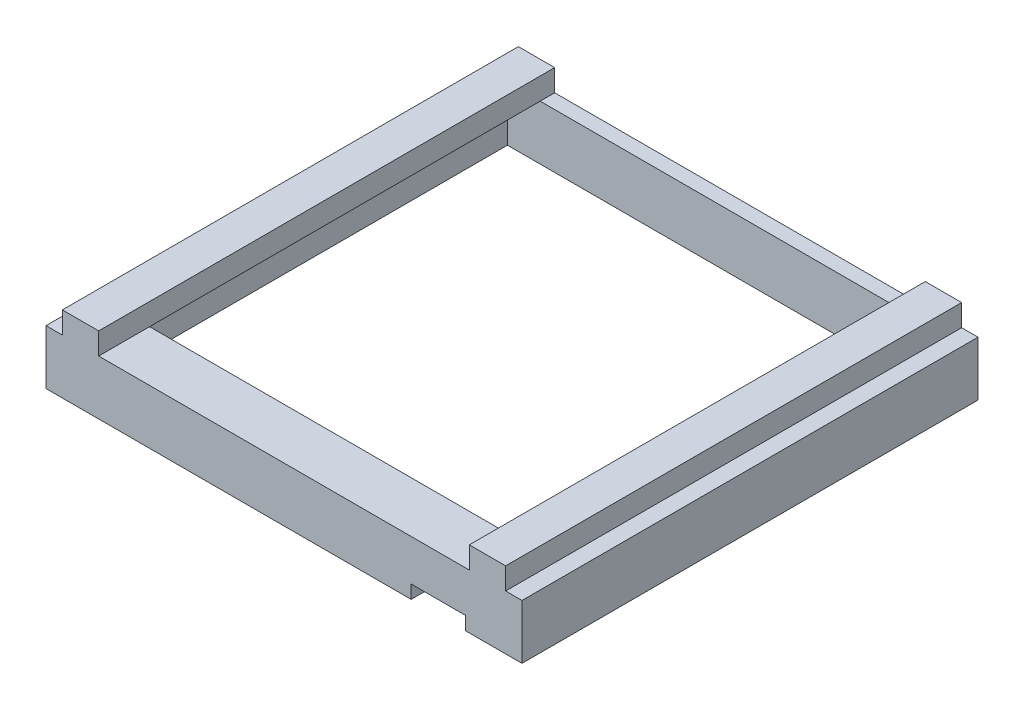
SolidWorks part; units mm, degrees
ref_plane "Front Plane" through (0, 0, 0) normal (0, 0, 1) x (1, 0, 0)
ref_plane "Top Plane" through (0, 0, 0) normal (0, 1, 0) x (1, 0, 0)
ref_plane "Right Plane" through (0, 0, 0) normal (1, 0, 0) x (0, 0, -1)
sketch "Sketch2" plane through (0, 0, 0) normal (0, 1, 0) x (1, 0, 0)
  line L0 (-98.2639, 59.75) -> (21.7361, 59.75)
  line L5 (-103.7639, -60.25) -> (27.2361, -60.25)
  line L6 (-103.7639, -60.25) -> (-103.7639, 65.25)
  line L7 (-103.7639, 65.25) -> (27.2361, 65.25)
  line L8 (27.2361, -60.25) -> (27.2361, 65.25)
  line L9 (-103.7639, -60.25) -> (27.2361, 65.25) construction
  line L10 (-103.7639, 65.25) -> (27.2361, -60.25) construction
  line L11 (21.7361, -54.75) -> (21.7361, 59.75)
  line L12 (-98.2639, -54.75) -> (21.7361, -54.75)
  line L13 (-98.2639, -54.75) -> (-98.2639, 59.75)
  line L14 (11.7361, -60.25) -> (11.7361, -54.75)
  line L15 (-3.2639, -54.75) -> (-3.2639, -60.25)
  point P0 (-38.2639, 2.5)
  dimension "D1" = 125.5
  dimension "D2" = 131
  dimension "D4" = 10
  dimension "D5" = 15
  dimension "D3" = 114.5
extrude "Boss-Extrude1" add sketch "Sketch2" along normal blind 15 contours L15 L12 L13 L0 L11 L14 L5 L8 L7 L6
sketch "Sketch8" plane through (0, 15, 0) normal (0, 1, 0) x (1, 0, 0)
  line L0 (-103.7639, -60.25) -> (-3.2639, -60.25) construction
  line L1 (-99.2639, -60.25) -> (-89.2639, -60.25)
  line L2 (-99.2639, -60.25) -> (-99.2639, -54.75)
  line L3 (-99.2639, -54.75) -> (-89.2639, -54.75)
  line L4 (-89.2639, -60.25) -> (-89.2639, -54.75)
  line L5 (-98.2639, -54.75) -> (-3.2639, -54.75) construction
  dimension "D1" = 4.5
  dimension "D2" = 10
extrude "Boss-Extrude2" add sketch "Sketch8" along normal blind 6
sketch "Sketch9" plane through (0, 0, 54.75) normal (0, 0, -1) x (-1, 0, 0)
  line L0 (90.2639, 16) -> (90.2639, 20)
  line L1 (89.2639, 15) -> (99.2639, 15)
  line L2 (89.2639, 15) -> (89.2639, 21)
  line L3 (89.2639, 21) -> (99.2639, 21)
  line L4 (99.2639, 15) -> (99.2639, 21)
  line L5 (90.2639, 20) -> (98.2639, 20)
  line L6 (98.2639, 16) -> (98.2639, 20)
  line L8 (90.2639, 16) -> (98.2639, 16) construction
  line L9 (90.2639, 16) -> (90.2639, 15)
  line L10 (98.2639, 16) -> (98.2639, 15)
  line M11 (98.2639, 15) -> (99.2639, 15)
  line M12 (99.2639, 15) -> (99.2639, 21)
  line M13 (99.2639, 21) -> (89.2639, 21)
  line M14 (89.2639, 21) -> (89.2639, 15)
  dimension "D1" = 1
extrude "Boss-Extrude3" add sketch "Sketch9" along normal blind 120 contours L6 L10 L1 L9 L0 L5 M11 M12 M13 M14
sketch "Sketch10" plane through (0, 15, 0) normal (0, 1, 0) x (1, 0, 0)
  line L0 (-103.7639, 65.25) -> (-99.2639, 65.25) construction
  line L1 (-90.2639, 65.25) -> (-98.2639, 65.25)
  line L2 (-90.2639, 65.25) -> (-90.2639, 59.75)
  line L3 (-90.2639, 59.75) -> (-98.2639, 59.75)
  line L4 (-98.2639, 65.25) -> (-98.2639, 59.75)
  point P6 (0, 0)
  point P9 (0, 0)
extrude "Boss-Extrude4" add sketch "Sketch10" along normal blind 5
sketch "Sketch11" plane through (-3.2639, 0, 0) normal (1, 0, 0) x (0, 0, -1)
  line L0 (-54.75, 15) -> (-54.75, 0) construction
  line L1 (-60.25, 15) -> (-54.75, 15)
  line L2 (-60.25, 15) -> (-60.25, 3.6654)
  line L3 (-60.25, 3.6654) -> (-54.75, 3.6654)
  line L4 (-54.75, 15) -> (-54.75, 3.6654)
extrude "Boss-Extrude5" add sketch "Sketch11" along normal blind 15 contours L2 L1 L4 L3
sketch "Sketch12" plane through (0, 15, 0) normal (0, 1, 0) x (1, 0, 0)
  line L0 (-89.2639, -60.25) -> (27.2361, -60.25) construction
  line L1 (22.7361, -60.25) -> (12.7361, -60.25)
  line L2 (22.7361, -60.25) -> (22.7361, -54.75)
  line L3 (22.7361, -54.75) -> (12.7361, -54.75)
  line L4 (12.7361, -60.25) -> (12.7361, -54.75)
  line L5 (-89.2639, -54.75) -> (21.7361, -54.75) construction
  dimension "D1" = 4.5
  dimension "D2" = 10
extrude "Boss-Extrude6" add sketch "Sketch12" along normal blind 6 contours L2 L1 L4 L3
sketch "Sketch13" plane through (0, 0, 54.75) normal (0, 0, -1) x (-1, 0, 0)
  line L0 (-21.7361, 16) -> (-21.7361, 20)
  line L1 (-22.7361, 15) -> (-12.7361, 15)
  line L2 (-22.7361, 15) -> (-22.7361, 21)
  line L3 (-22.7361, 21) -> (-12.7361, 21)
  line L4 (-12.7361, 15) -> (-12.7361, 21)
  line L5 (-21.7361, 20) -> (-13.7361, 20)
  line L6 (-13.7361, 16) -> (-13.7361, 20)
  line L8 (-21.7361, 16) -> (-21.7361, 15)
  line L9 (-13.7361, 16) -> (-13.7361, 15)
  line L11 (-21.7361, 16) -> (-13.7361, 16) construction
  line M21 (-12.7361, 15) -> (-12.7361, 21)
  line M22 (-12.7361, 21) -> (-22.7361, 21)
  line M23 (-22.7361, 21) -> (-22.7361, 15)
  line M24 (-22.7361, 15) -> (-21.7361, 15)
  dimension "D1" = 1
extrude "Boss-Extrude7" add sketch "Sketch13" along normal blind 120 contours L6 L9 L1 L8 L0 L5 M21 M22 M23 M24
sketch "Sketch14" plane through (0, 15, 0) normal (0, 1, 0) x (1, 0, 0)
  line L0 (22.7361, 65.25) -> (27.2361, 65.25) construction
  line L1 (22.7361, 65.25) -> (13.7361, 65.25)
  line L2 (22.7361, 65.25) -> (22.7361, 59.75)
  line L3 (22.7361, 59.75) -> (13.7361, 59.75)
  line L4 (13.7361, 65.25) -> (13.7361, 59.75)
  line L5 (22.7361, -60.25) -> (22.7361, 65.25) construction
  point P6 (0, 0)
  point P7 (0, 0)
  point P10 (0, 0)
  point P14 (0, 0)
extrude "Boss-Extrude8" add sketch "Sketch14" along normal blind 6
sketch "Sketch15" plane through (0, 0, 54.75) normal (0, 0, -1) x (-1, 0, 0)
  line L6 (-13.7361, 15) -> (90.2639, 15)
  line L7 (-13.7361, 15) -> (-13.7361, 12)
  line L8 (-13.7361, 12) -> (90.2639, 12)
  line L9 (90.2639, 15) -> (90.2639, 12)
  dimension "D1" = 3
extrude "Boss-Extrude11" add sketch "Sketch15" along normal blind 8.5
sketch "Sketch17" plane through (0, 0, -59.75) normal (0, 0, 1) x (1, 0, 0)
  line L20 (-98.2639, 0) -> (21.7361, 0)
  line L21 (21.7361, 0) -> (21.7361, 20)
  line L22 (21.7361, 20) -> (13.7361, 20)
  line L23 (13.7361, 20) -> (13.7361, 15)
  line L24 (13.7361, 15) -> (12.7361, 15)
  line L25 (12.7361, 15) -> (-89.2639, 15)
  line L26 (-89.2639, 15) -> (-90.2639, 15)
  line L27 (-90.2639, 15) -> (-90.2639, 20)
  line L28 (-90.2639, 20) -> (-98.2639, 20)
  line L29 (-98.2639, 20) -> (-98.2639, 0)
  line L30 (-98.2639, 0) -> (21.7361, 0)
  line L31 (21.7361, 0) -> (21.7361, 20)
  line L32 (21.7361, 20) -> (13.7361, 20)
  line L33 (13.7361, 20) -> (13.7361, 15)
  line L34 (13.7361, 15) -> (12.7361, 15)
  line L35 (12.7361, 15) -> (-89.2639, 15)
  line L36 (-89.2639, 15) -> (-90.2639, 15)
  line L37 (-90.2639, 15) -> (-90.2639, 20)
  line L38 (-90.2639, 20) -> (-98.2639, 20)
  line L39 (-98.2639, 20) -> (-98.2639, 0)
  dimension "D1" = 0
extrude "Cut-Extrude1" cut sketch "Sketch17" against normal blind 1.5 contours L30 L31 L32 L33 L34 L35 L36 L37 L38 L39
